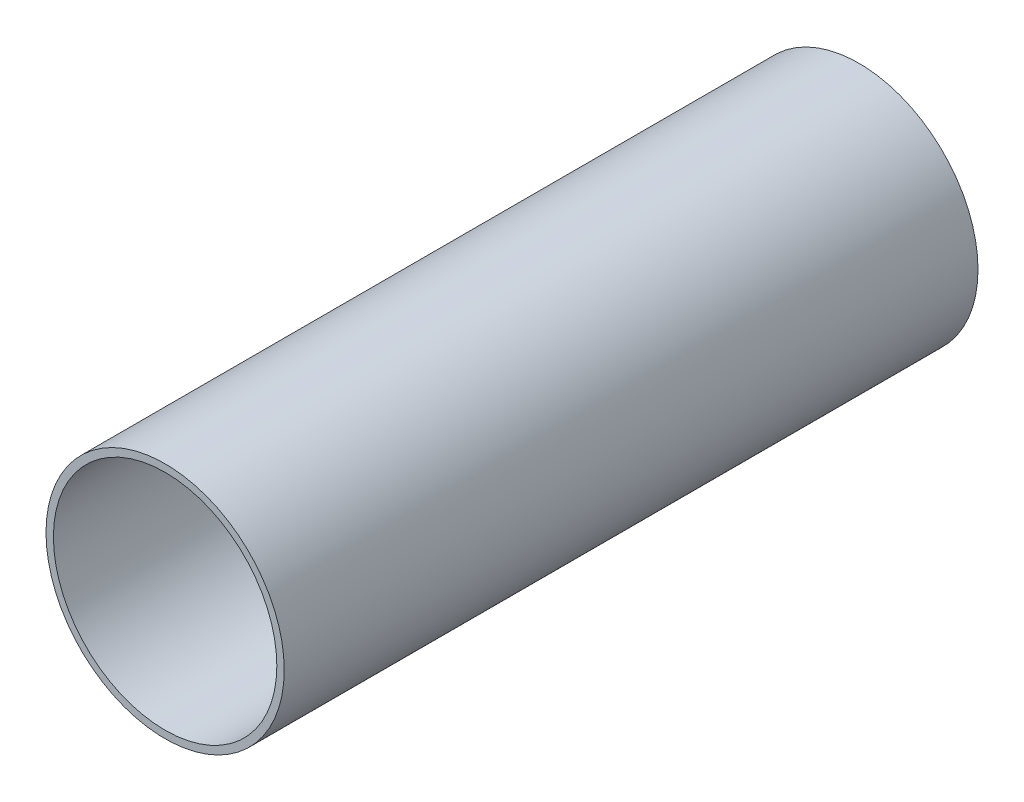
SolidWorks part; units mm, degrees
ref_plane "Front Plane" through (0, 0, 0) normal (0, 0, 1) x (1, 0, 0)
ref_plane "Top Plane" through (0, 0, 0) normal (0, 1, 0) x (1, 0, 0)
ref_plane "Right Plane" through (0, 0, 0) normal (1, 0, 0) x (0, 0, -1)
sketch "Sketch1" plane through (0, 0, 0) normal (0, 0, 1) x (1, 0, 0)
  circle A0 centre (0, 0) radius 95
  circle A1 centre (0, 0) radius 101.3
extrude "Boss-Extrude1" add sketch "Sketch1" along normal blind 590
